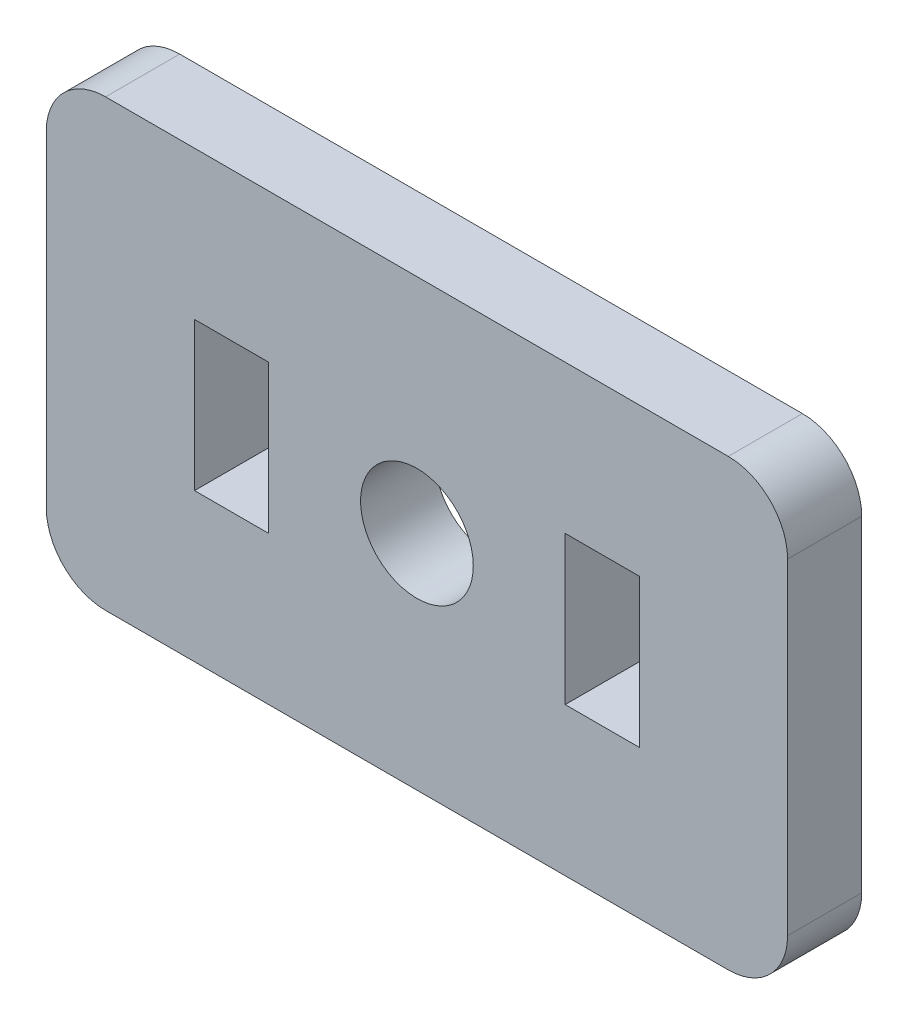
SolidWorks part; units mm, degrees
ref_plane "Front Plane" through (0, 0, 0) normal (0, 0, 1) x (1, 0, 0)
ref_plane "Top Plane" through (0, 0, 0) normal (0, 1, 0) x (1, 0, 0)
ref_plane "Right Plane" through (0, 0, 0) normal (1, 0, 0) x (0, 0, -1)
sketch "Sketch1" plane through (0, 0, 0) normal (0, 0, 1) x (1, 0, 0)
  line L0 (0, 9.525) -> (0, -9.525) construction
  line L1 (-9.525, -9.525) -> (9.525, -9.525)
  line L2 (-9.525, -9.525) -> (-9.525, 9.525)
  line L3 (-9.525, 9.525) -> (9.525, 9.525)
  line L4 (9.525, -9.525) -> (9.525, 9.525)
  line L5 (-9.525, -9.525) -> (9.525, 9.525) construction
  line L6 (-9.525, 9.525) -> (9.525, -9.525) construction
  line L11 (-15.875, -15.875) -> (-15.875, 15.875)
  line L12 (-15.875, 15.875) -> (15.875, 15.875)
  line L17 (15.875, -15.875) -> (15.875, 15.875)
  line L18 (-15.875, -15.875) -> (15.875, -15.875)
  line L19 (-9.525, 9.525) -> (-15.875, 9.525)
  line L20 (9.525, 9.525) -> (15.875, 9.525)
  line L21 (9.525, -9.525) -> (15.875, -9.525)
  line L22 (-9.525, -9.525) -> (-15.875, -9.525)
  circle A0 centre (0, 0) radius 2.413
  point P0 (0, 0)
  dimension "D4" = 4.826
  dimension "D1" = 19.05
  dimension "D2" = 6.35
extrude "Boss-Extrude1" add sketch "Sketch1" along normal blind 3.175 contours L22 L2 L19 L11 | L1 L4 L3 L2 A0 | L4 L21 L17 L20
fillet "Fillet1" radius 2.54 4 edges at (-15.875, -9.525, 1.5875) (15.875, -9.525, 1.5875) (15.875, 9.525, 1.5875) (-15.875, 9.525, 1.5875)
sketch "Sketch2" plane through (0, 0, 3.175) normal (0, 0, 1) x (1, 0, 0)
  line L0 (-6.35, 0) -> (6.35, 0) construction
  line L1 (6.35, 3.175) -> (9.525, 3.175)
  line L2 (6.35, 3.175) -> (6.35, -3.175)
  line L3 (6.35, -3.175) -> (9.525, -3.175)
  line L4 (9.525, 3.175) -> (9.525, -3.175)
  line L5 (-9.525, 3.175) -> (-6.35, 3.175)
  line L6 (-9.525, 3.175) -> (-9.525, -3.175)
  line L7 (-9.525, -3.175) -> (-6.35, -3.175)
  line L8 (-6.35, 3.175) -> (-6.35, -3.175)
  point P9 (6.35, 0)
  point P12 (0, 0)
  dimension "D1" = 3.175
  dimension "D2" = 12.7
  dimension "D3" = 6.35
extrude "Cut-Extrude1" cut sketch "Sketch2" against normal up to next
